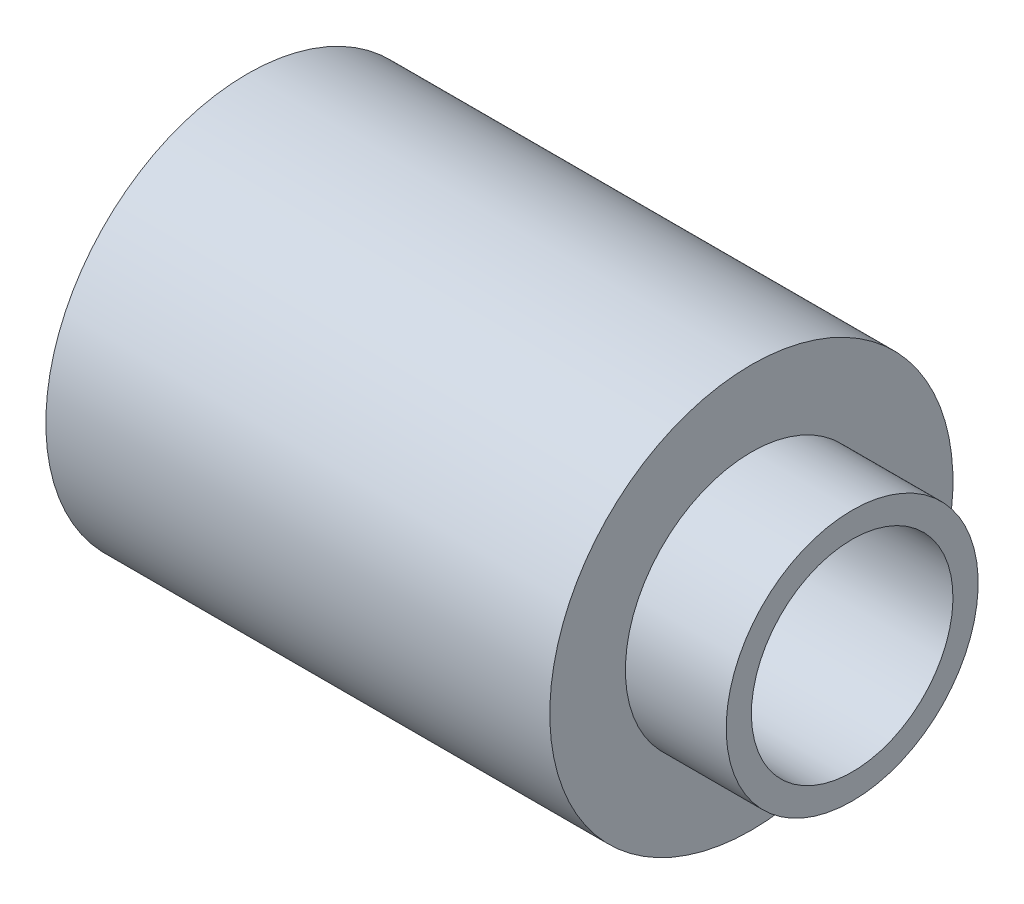
SolidWorks part; units mm, degrees
ref_plane "Front Plane" through (0, 0, 0) normal (0, 0, 1) x (1, 0, 0)
ref_plane "Top Plane" through (0, 0, 0) normal (0, 1, 0) x (1, 0, 0)
ref_plane "Right Plane" through (0, 0, 0) normal (1, 0, 0) x (0, 0, -1)
sketch "Sketch2" plane through (0, 0, 0) normal (0, 0, 1) x (1, 0, 0)
  line L0 (0, 0) -> (-12, 0)
  line L1 (-12, 0) -> (-12, 4)
  line L2 (-12, 4) -> (-2, 4)
  line L3 (-2, 4) -> (-2, 2.5)
  line L4 (-2, 2.5) -> (0, 2.5)
  line L5 (0, 2.5) -> (0, 0)
  dimension "D1" = 4
  dimension "D2" = 10
  dimension "D3" = 2.5
  dimension "D4" = 1.5
  dimension "D5" = 12
revolve "Revolve1" add sketch "Sketch2" angle 360 about L0
sketch "Sketch3" plane through (0, 0, 0) normal (1, 0, 0) x (0, 0, -1)
  circle A0 centre (0, 0) radius 2
  dimension "D1" = 4
extrude "Cut-Extrude1" cut sketch "Sketch3" against normal through all
